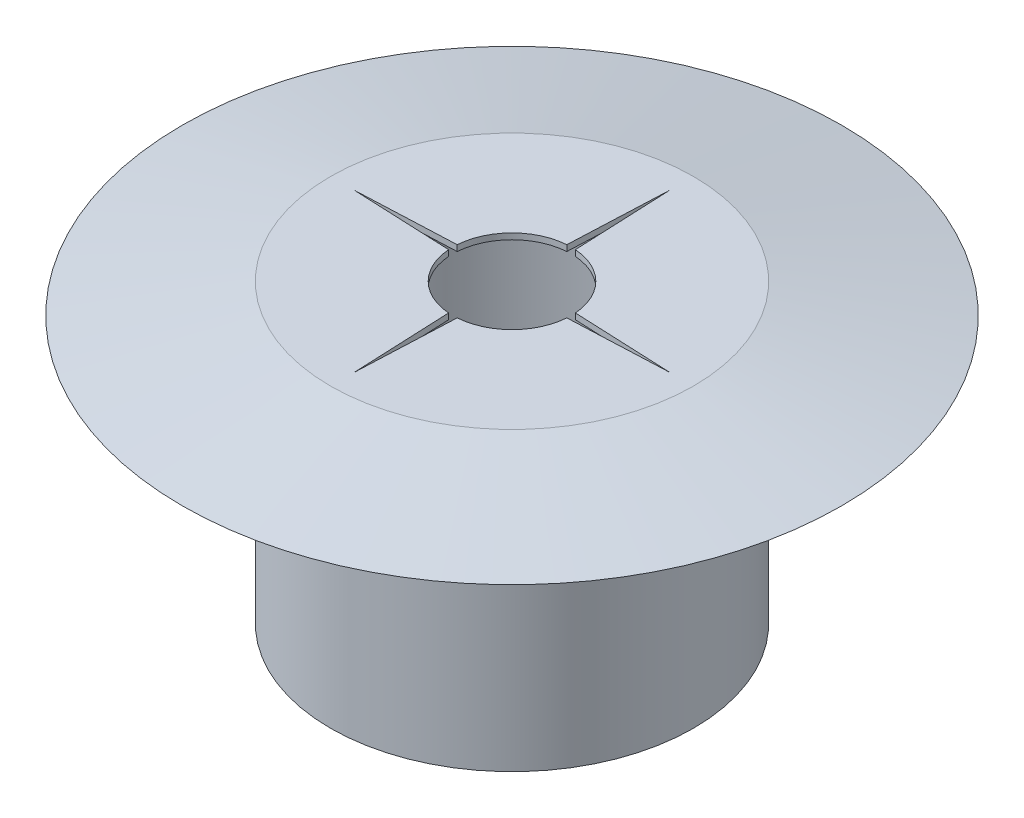
SolidWorks part; units mm, degrees
ref_plane "Alzado" through (0, 0, 0) normal (0, 0, 1) x (1, 0, 0)
ref_plane "Planta" through (0, 0, 0) normal (0, 1, 0) x (1, 0, 0)
ref_plane "Vista lateral" through (0, 0, 0) normal (1, 0, 0) x (0, 0, -1)
sketch "Croquis1" plane through (0, 0, 0) normal (0, 0, 1) x (1, 0, 0)
  line L0 (0, 0) -> (0, 16.2) construction
  line L1 (-10.9, 20) -> (-10.9, 0)
  line L2 (-10.9, 0) -> (-12.25, 0)
  line L3 (-12.25, 0) -> (-12.25, 18)
  line L4 (-12.25, 18) -> (-22.25, 18)
  line L5 (-22.25, 18) -> (-12.25, 20)
  line L6 (-12.25, 20) -> (-10.9, 20)
  dimension "D1" = 1.35
  dimension "D2" = 2
  dimension "D3" = 12.25
  dimension "D4" = 10
  dimension "D5" = 20
revolve "Revolución1" add sketch "Croquis1" angle 360 about L0
sketch "Croquis3" plane through (0, 20, 0) normal (0, 1, 0) x (1, 0, 0)
  line L0 (0, 0) -> (0, -10.9) construction
  line L2 (0, 0) -> (7.7075, -7.7075) construction
  line L4 (0, 0) -> (10.9, 0) construction
  line L5 (0.2901, -3.9895) -> (0, -10.6398)
  line L6 (3.9895, -0.2901) -> (10.6398, 0)
  line L7 (-0.2901, -3.9895) -> (0, -10.6398)
  line L8 (-3.9895, -0.2901) -> (-10.6398, 0)
  line L9 (-3.9895, 0.2901) -> (-10.6398, 0)
  line L10 (-0.2901, 3.9895) -> (0, 10.6398)
  line L11 (0.2901, 3.9895) -> (0, 10.6398)
  line L12 (3.9895, 0.2901) -> (10.6398, 0)
  circle A1 centre (0, 0) radius 4 construction
  arc A2 (3.9895, -0.2901) -> (0.2901, -3.9895) centre (0, 0) cw
  circle A3 centre (0, 0) radius 10.9 construction
  arc A4 (10.9, 0) -> (0, -10.9) centre (0, 0) cw
  arc A5 (0, -10.9) -> (-10.9, 0) centre (0, 0) cw
  arc A6 (-0.2901, -3.9895) -> (-3.9895, -0.2901) centre (0, 0) cw
  arc A7 (-10.9, 0) -> (0, 10.9) centre (0, 0) cw
  arc A8 (-3.9895, 0.2901) -> (-0.2901, 3.9895) centre (0, 0) cw
  arc A9 (0, 10.9) -> (10.9, 0) centre (0, 0) cw
  arc A10 (0.2901, 3.9895) -> (3.9895, 0.2901) centre (0, 0) cw
  point P15 (0.2901, -3.9895)
  dimension "D1" = 8
  dimension "D2" = 4
extrude "Saliente-Extruir2" add sketch "Croquis3" against normal blind 0.4 contours L5 L11 A10 L12 L6 A2 L7 A6 L8 L9 A8 L10
